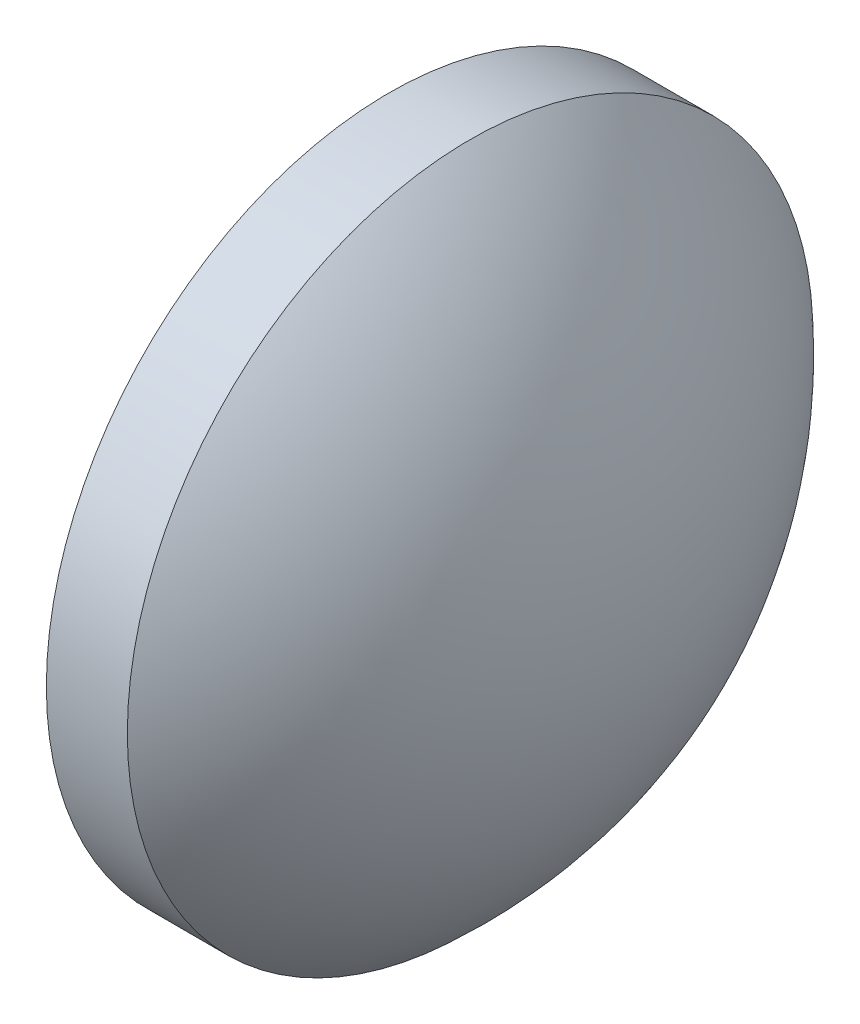
SolidWorks part; units mm, degrees
ref_plane "前视基准面" through (0, 0, 0) normal (0, 0, 1) x (1, 0, 0)
ref_plane "上视基准面" through (0, 0, 0) normal (0, 1, 0) x (1, 0, 0)
ref_plane "右视基准面" through (0, 0, 0) normal (1, 0, 0) x (0, 0, -1)
sketch "草图1" plane through (0, 0, 0) normal (0, 0, 1) x (1, 0, 0)
  line L0 (407.01, 28.2908) -> (414.5284, 28.2908) construction
  line L1 (409.2705, 28.2908) -> (409.2705, 34.6408)
  line L2 (409.2705, 34.6408) -> (410.7705, 34.6408)
  line L3 (413.5705, 28.2908) -> (409.2705, 28.2908)
  arc A0 (413.5705, 28.2908) -> (410.7705, 34.6408) centre (404.9701, 28.2908) ccw
revolve "旋转1" add sketch "草图1" angle 360 about L0
